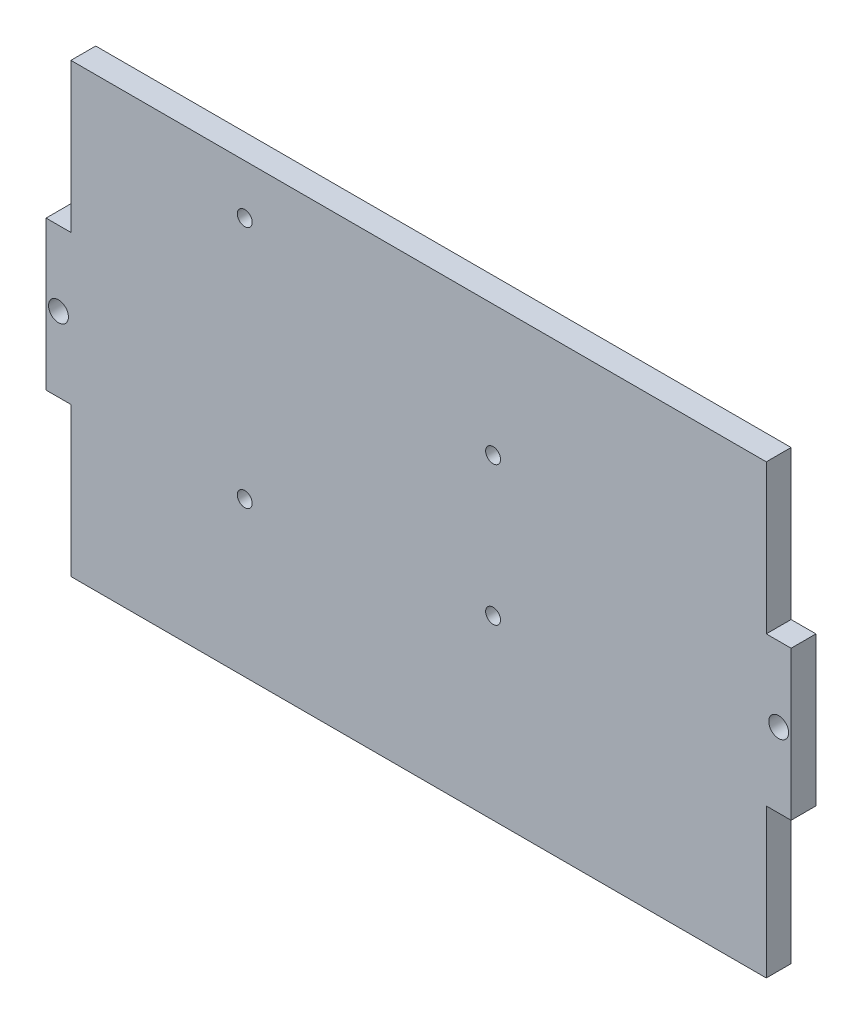
SolidWorks part; units mm, degrees
ref_plane "Front Plane" through (0, 0, 0) normal (0, 0, 1) x (1, 0, 0)
ref_plane "Top Plane" through (0, 0, 0) normal (0, 1, 0) x (1, 0, 0)
ref_plane "Right Plane" through (0, 0, 0) normal (1, 0, 0) x (0, 0, -1)
sketch "Sketch1" plane through (0, 0, 0) normal (0, 0, 1) x (1, 0, 0)
  line L0 (0, 47.2557) -> (0, -1078.3889) construction
  line L1 (-73.3854, 0) -> (102.8507, 0) construction
  line L2 (-75, -15) -> (-70, -15)
  line L3 (-75, 15) -> (-70, 15)
  line L4 (-70, 45) -> (-70, 15)
  line L5 (70, 45) -> (70, 15)
  line L6 (-75, 15) -> (-75, -15)
  line L7 (75, 15) -> (75, -15)
  line L8 (-70, -45) -> (70, -45)
  line L9 (-70, 45) -> (70, 45)
  line L10 (-70, -15) -> (-70, -45)
  line L11 (-73.3854, 15) -> (102.8507, 15) construction
  line L12 (-73.3854, -15) -> (102.8507, -15) construction
  line L13 (-73.3854, -45) -> (102.8507, -45) construction
  line L14 (-73.3854, 45) -> (102.8507, 45) construction
  line L15 (-75, 47.2557) -> (-75, -1078.3889) construction
  line L16 (-70, 47.2557) -> (-70, -1078.3889) construction
  line L17 (75, 47.2557) -> (75, -1078.3889) construction
  line L18 (70, 47.2557) -> (70, -1078.3889) construction
  line L19 (70, -15) -> (70, -45)
  line L20 (70, 15) -> (75, 15)
  line L21 (70, -15) -> (75, -15)
  dimension "D1" = 15
  dimension "D2" = 15
  dimension "D3" = 70
  dimension "D4" = 70
  dimension "D5" = 75
  dimension "D6" = 75
  dimension "D7" = 45
  dimension "D8" = 45
extrude "Boss-Extrude1" add sketch "Sketch1" along normal blind 5
sketch "Sketch2" plane through (0, 0, 5) normal (0, 0, 1) x (1, 0, 0)
  line L0 (-35, 35) -> (-35, -14) construction
  line L1 (15, 18.66) -> (15, -9.34) construction
  line L2 (70, 45) -> (-70, 45) construction
  line L4 (70, 15) -> (70, 45) construction
  circle A0 centre (15, 18.66) radius 1.5
  circle A1 centre (15, -9.34) radius 1.5
  circle A2 centre (-35, 35) radius 1.5
  circle A3 centre (-35, -14) radius 1.5
  dimension "D1" = 3
  dimension "D2" = 3
  dimension "D3" = 3
  dimension "D4" = 3
  dimension "D5" = 50
  dimension "D6" = 28
  dimension "D7" = 49
  dimension "D8" = 10
  dimension "D9" = 55
  dimension "D10" = 4.66
extrude "Cut-Extrude1" cut sketch "Sketch2" against normal blind 10
sketch "Sketch3" plane through (0, 0, 5) normal (0, 0, 1) x (1, 0, 0)
  line L0 (-72.5, 15) -> (-72.5, -15) construction
  line L1 (-70, 15) -> (-75, 15) construction
  line L2 (-75, -15) -> (-70, -15) construction
  line L3 (72.5, 15) -> (72.5, -15) construction
  line L4 (75, 15) -> (70, 15) construction
  line L5 (70, -15) -> (75, -15) construction
  circle A0 centre (-72.5, 0) radius 2
  circle A1 centre (72.5, 0) radius 2
  dimension "D1" = 4
  dimension "D2" = 4
extrude "Cut-Extrude2" cut sketch "Sketch3" against normal blind 10
